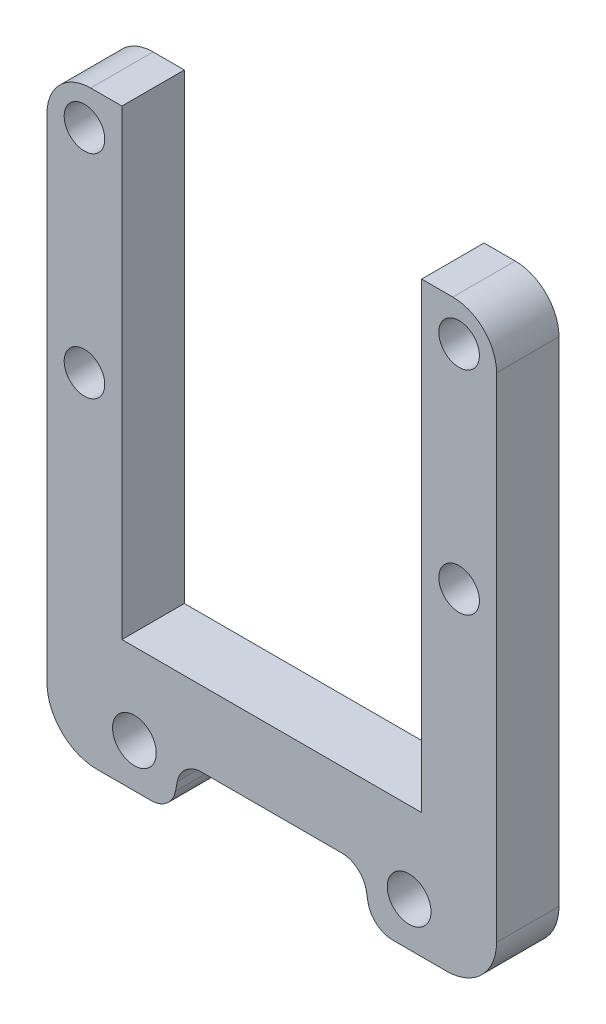
SolidWorks part; units mm, degrees
ref_plane "Plan de face" through (0, 0, 0) normal (0, 0, 1) x (1, 0, 0)
ref_plane "Plan de dessus" through (0, 0, 0) normal (0, 1, 0) x (1, 0, 0)
ref_plane "Plan de droite" through (0, 0, 0) normal (1, 0, 0) x (0, 0, -1)
sketch "Esquisse1" plane through (0, 0, 0) normal (0, 0, 1) x (1, 0, 0)
  line L0 (24, 110) -> (24, 36)
  line L1 (24, 36) -> (0, 36)
  line L7 (0, 24) -> (14.5, 24)
  line L8 (14.5, 24) -> (16.055, 16)
  line L9 (16.055, 16) -> (36, 16)
  line L10 (36, 16) -> (36, 110)
  line L11 (36, 110) -> (24, 110)
  line L12 (0, 36) -> (0, 24)
  line L13 (0, -0.15) -> (0, 72.4519) construction
  circle A0 centre (30, 104) radius 3.25
  circle A1 centre (22, 23) radius 3.5
  circle A3 centre (30, 70) radius 3.25
  point P19 (30, 110)
  dimension "D9" = 7
  dimension "D10" = 6
  dimension "D14" = 6.5
  dimension "D1" = 12
  dimension "D2" = 24
  dimension "D3" = 101
  dimension "D4" = 24
  dimension "D5" = 12
  dimension "D6" = 74
  dimension "D7" = 8
  dimension "D8" = 14.5
  dimension "D11" = 34
  dimension "D12" = 1
  dimension "D13" = 22
extrude "Boss.-Extru.1" add sketch "Esquisse1" along normal blind 10
mirror "Symétrie2" about plane through (0, 36, 10) normal (1, 0, 0) of "Boss.-Extru.1"
fillet "Congé1" radius 4 4 edges at (16.055, 16, 5) (-16.055, 16, 5) (-14.5, 24, 5) (14.5, 24, 5)
fillet "Congé2" radius 8 2 edges at (-36, 16, 5) (36, 16, 5)
fillet "Congé3" radius 7 2 edges at (36, 110, 5) (-36, 110, 5)
sketch "Esquisse2" plane through (0, 0, 0) normal (0, 0, 1) x (1, 0, 0)
  line L0 (0, 36) -> (28, 36)
  line L1 (24, 36) -> (-24, 36) construction
  line L2 (33, 41) -> (33, 68.75)
  line L4 (36, 103) -> (36, 39)
  line L5 (31, 34) -> (0, 34)
  line L6 (0, 34) -> (0, 36)
  line L7 (30, 107.25) -> (30, 109.9282)
  line L8 (36, 24) -> (36, 103) construction
  line L9 (33, 71.25) -> (33, 102.75)
  circle A0 centre (30, 104) radius 3.25 construction
  arc A1 (33, 102.75) -> (30, 107.25) centre (30, 104) ccw
  arc A2 (36, 103) -> (29, 110) centre (29, 103) ccw construction
  arc A3 (36, 103) -> (30, 109.9282) centre (29, 103) ccw
  circle A4 centre (30, 70) radius 3.25 construction
  arc A5 (33, 68.75) -> (33, 71.25) centre (30, 70) ccw
  arc A6 (36, 39) -> (31, 34) centre (31, 39) cw
  arc A7 (28, 36) -> (33, 41) centre (28, 41) ccw
  dimension "D2" = 5
  dimension "D1" = 2
  dimension "D3" = 33
